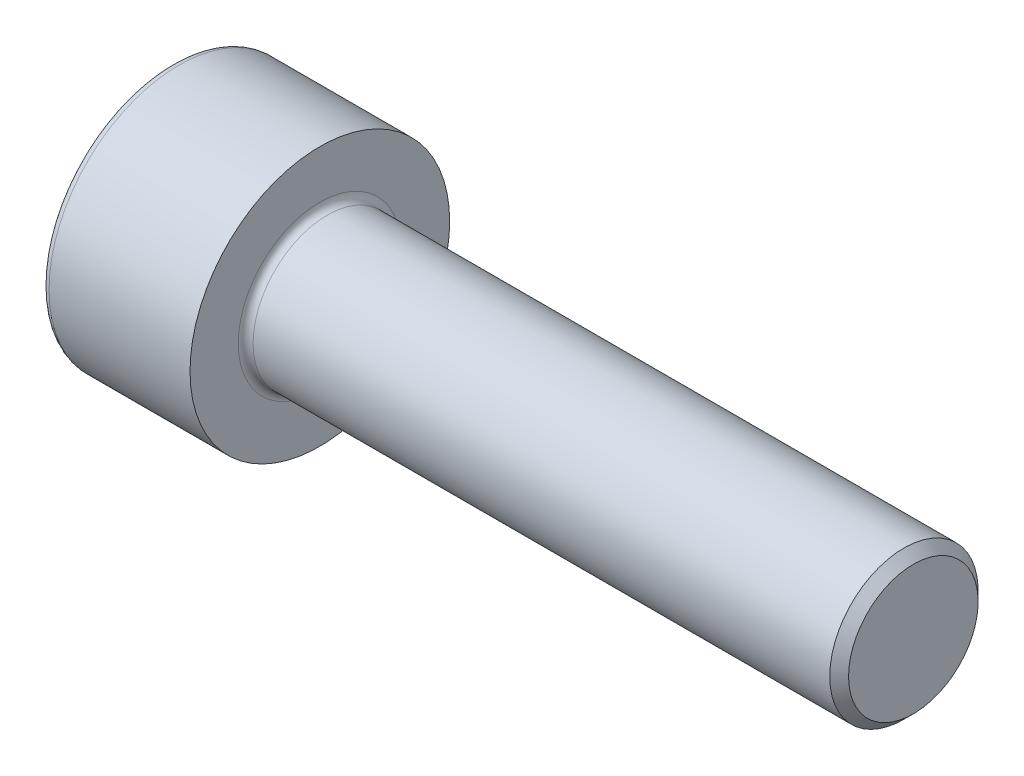
SolidWorks part; units mm, degrees
ref_plane "Front" through (0, 0, 0) normal (0, 0, 1) x (1, 0, 0)
ref_plane "Top" through (0, 0, 0) normal (0, 1, 0) x (1, 0, 0)
ref_plane "Right" through (0, 0, 0) normal (1, 0, 0) x (0, 0, -1)
sketch "Sketch1" plane through (0, 0, 0) normal (0, 0, 1) x (1, 0, 0)
  line L0 (15.7465, 2) -> (0.2, 2)
  line L1 (-4, 3.3) -> (-4, 0)
  line L2 (0, 3.5) -> (-3.8, 3.5)
  line L3 (0, 2.2) -> (0, 3.5)
  line L4 (16, 1.7465) -> (16, 0)
  line L5 (16, 1.7465) -> (15.7465, 2)
  line L6 (-4, 0) -> (0, 0) construction
  line L7 (-4, 0) -> (16, 0)
  arc A0 (-3.8, 3.5) -> (-4, 3.3) centre (-3.8, 3.3) ccw
  arc A1 (0, 2.2) -> (0.2, 2) centre (0.2, 2.2) ccw
  point P12 (0, 2.85)
  dimension "D5" = 0.2
  dimension "D1" = 4
  dimension "D2" = 7
  dimension "D3" = 135
  dimension "D4" = 0.3585
  dimension "D6" = 16
  dimension "D7" = 4
revolve "Revolve1" add sketch "Sketch1" angle 360 about L7
sketch "Sketch2" plane through (-4, 0, 0) normal (-1, 0, 0) x (0, 0, 1)
  line L7 (1.535, 0.8862) -> (0, 1.7725)
  line L8 (0, 1.7725) -> (-1.535, 0.8862)
  line L9 (-1.535, 0.8862) -> (-1.535, -0.8862)
  line L10 (-1.535, -0.8862) -> (0, -1.7725)
  line L11 (0, -1.7725) -> (1.535, -0.8862)
  line L12 (1.535, -0.8862) -> (1.535, 0.8862)
  circle A0 centre (0, 0) radius 1.535 construction
  dimension "D1" = 3.07
extrude "Cut-Extrude1" cut sketch "Sketch2" against normal blind 2
